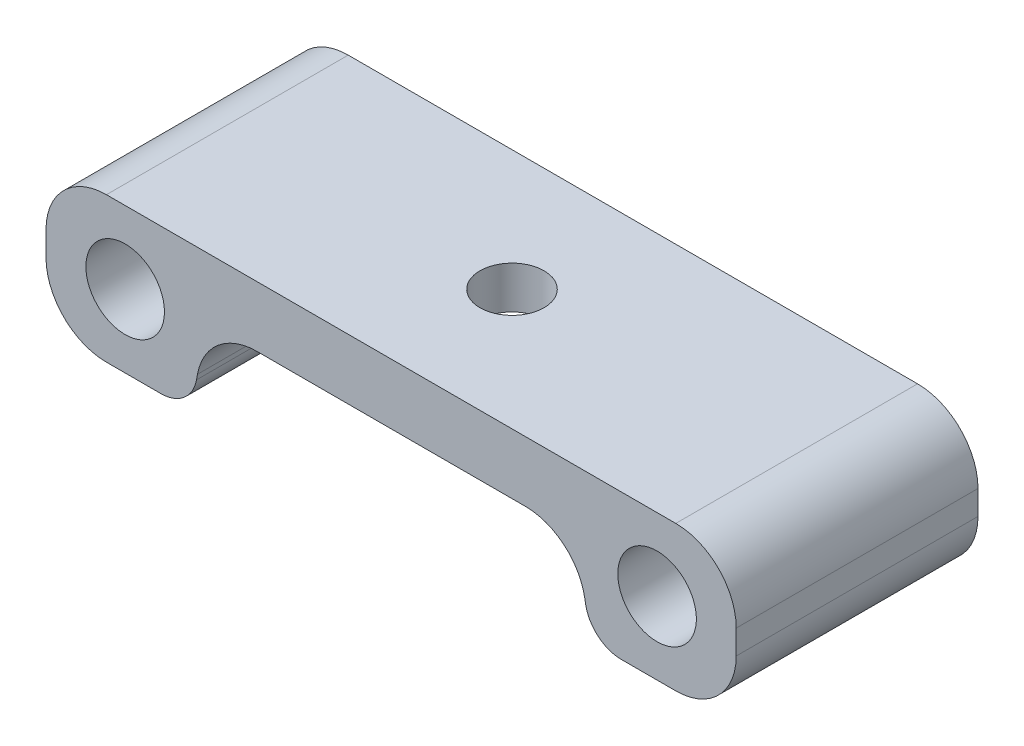
SolidWorks part; units mm, degrees
ref_plane "Plan de face" through (0, 0, 0) normal (0, 0, 1) x (1, 0, 0)
ref_plane "Plan de dessus" through (0, 0, 0) normal (0, 1, 0) x (1, 0, 0)
ref_plane "Plan de droite" through (0, 0, 0) normal (1, 0, 0) x (0, 0, -1)
sketch "Esquisse1" plane through (0, 0, 0) normal (0, 0, 1) x (1, 0, 0)
  line L0 (0, 0) -> (-15.2657, 0)
  line L1 (-15.2657, 0) -> (-16.5481, -7)
  line L2 (-16.5481, -7) -> (-28.5481, -7)
  line L3 (-28.5481, -7) -> (-28.5481, 5)
  line L4 (-28.5481, 5) -> (0, 5)
  line L6 (0, 5) -> (0, 0)
  line L7 (-15, -4.099) -> (-21.8, -41.2188) construction
  circle A0 centre (-22, -1) radius 3.25
  point P11 (-28.5481, -1)
  point P19 (-22, -1)
  dimension "D4" = 6.5
  dimension "D1" = 5
  dimension "D2" = 12
  dimension "D3" = 12
  dimension "D5" = 1
  dimension "D6" = 22
extrude "Boss.-Extru.1" add sketch "Esquisse1" along normal mid plane 20
mirror "Symétrie1" about plane through (0, 5, 10) normal (-1, 0, 0) of "Boss.-Extru.1"
fillet "Congé1" radius 5 6 edges at (-15.2657, 0, 0) (-28.5481, -7, 0) (-28.5481, 5, 0) (15.2657, 0, 0) (28.5481, -7, 0) (28.5481, 5, 0)
fillet "Congé2" radius 3 2 edges at (-16.5481, -7, 0) (16.5481, -7, 0)
sketch "Esquisse2" plane through (0, 0, 0) normal (0, -1, 0) x (1, 0, 0)
  circle A0 centre (0, 0) radius 6
  dimension "D1" = 12
extrude "Enlèv. mat.-Extru.1" cut sketch "Esquisse2" against normal blind 1.5
sketch "Esquisse3" plane through (0, 5, 0) normal (0, 1, 0) x (1, 0, 0)
  circle A0 centre (0, 0) radius 2.65
  dimension "D1" = 5.3
extrude "Enlèv. mat.-Extru.2" cut sketch "Esquisse3" against normal through all
sketch "Esquisse4" plane through (0, 5, 0) normal (0, 1, 0) x (1, 0, 0)
  circle A0 centre (0, 0) radius 5.25
  dimension "D1" = 10.5
extrude "Enlèv. mat.-Extru.3" [suppressed] cut sketch "Esquisse4" against normal blind 1
